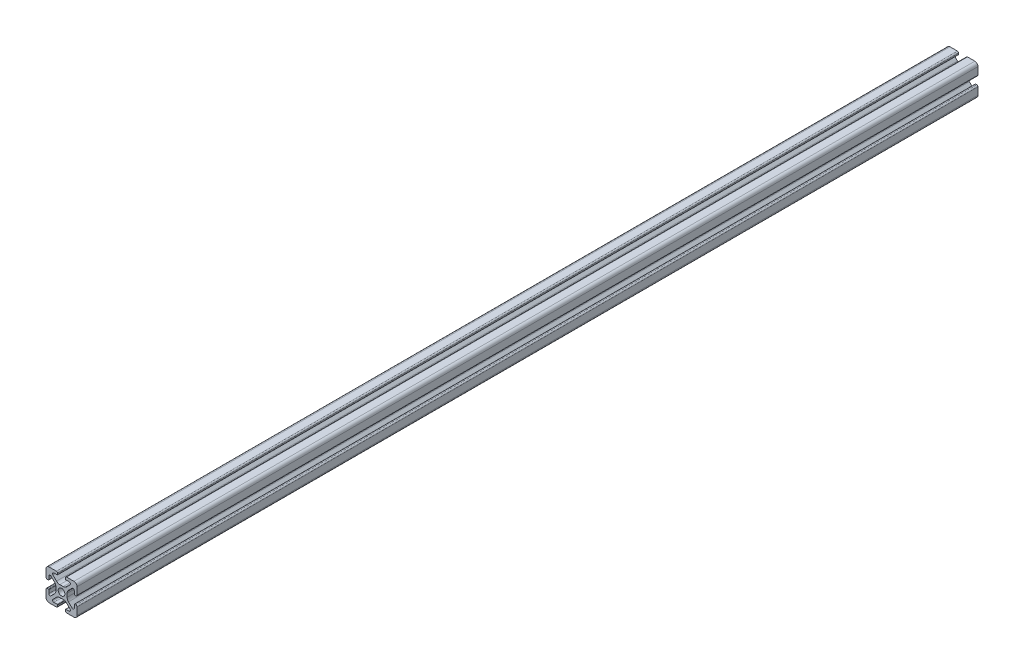
SolidWorks part; units mm, degrees
ref_plane "Front Plane" through (0, 0, 0) normal (0, 0, 1) x (1, 0, 0)
ref_plane "Top Plane" through (0, 0, 0) normal (0, 1, 0) x (1, 0, 0)
ref_plane "Right Plane" through (0, 0, 0) normal (1, 0, 0) x (0, 0, -1)
sketch "Sketch1" plane through (0, 0, 0) normal (0, 0, 1) x (1, 0, 0)
  line L0 (0, 10) -> (0, -10) construction
  line L1 (10, 0) -> (-10, 0) construction
  line L2 (-2.5, 10) -> (2.5, 10) construction
  line L3 (-5.75, 8.2) -> (5.75, 8.2) construction
  circle A0 centre (0, 0) radius 2.15 construction
  point P4 (0, 0)
  point P8 (0, 0)
  point P10 (0, 3.6)
  point P14 (0, 10)
  point P17 (0, 8.2)
  dimension "Thru Hole" = 4.3
  dimension "Height" = 20
  dimension "T Slot Depth" = 6.4
  dimension "T Slot Top Width" = 5
  dimension "T Slot Max Width" = 11.5
  dimension "Wall" = 1.8
sketch "Sketch2" plane through (0, 0, 0) normal (1, 0, 0) x (0, 0, -1)
  line L0 (152.4, 0) -> (-152.4, 0) construction
  point P4 (0, 0)
  dimension "D1" = 304.8
sketch "Sketch3" plane through (0, 0, 0) normal (0, 0, 1) x (1, 0, 0)
  line L0 (3.2874, 10) -> (8, 10)
  line L1 (10, 8) -> (10, -8) construction
  line L2 (8, -10) -> (-8, -10) construction
  line L3 (-10, 10) -> (10, -10) construction
  line L4 (2.5, 9.2126) -> (2.5, 8.5048)
  line L5 (-5.75, 8.2) -> (5.75, 8.2) construction
  line L6 (2.8048, 8.2) -> (4.9118, 8.2)
  line L7 (5.5045, 6.7691) -> (3.2141, 4.4787)
  line L8 (1.0928, 3.6) -> (-1.0928, 3.6)
  line L9 (0, 10) -> (0, -10) construction
  line L10 (5.75, 8.2) -> (5.75, 0) construction
  line L11 (10, 0) -> (-10, 0) construction
  line L12 (0, 0) -> (0, 10) construction
  line L13 (-2.5, 9.2126) -> (-2.5, 8.5048)
  line L14 (-5.5045, 6.7691) -> (-3.2141, 4.4787)
  line L15 (-2.8048, 8.2) -> (-4.9118, 8.2)
  line L16 (-3.2874, 10) -> (-8, 10)
  line L17 (0, 0) -> (-10, 0) construction
  line L18 (-10, 3.2874) -> (-10, 8)
  line L19 (-8.2, 2.8048) -> (-8.2, 4.9118)
  line L20 (-6.7691, 5.5045) -> (-4.4787, 3.2141)
  line L21 (-9.2126, 2.5) -> (-8.5048, 2.5)
  line L22 (-3.6, -1.0928) -> (-3.6, 1.0928)
  line L23 (-6.7691, -5.5045) -> (-4.4787, -3.2141)
  line L24 (-8.2, -2.8048) -> (-8.2, -4.9118)
  line L25 (-9.2126, -2.5) -> (-8.5048, -2.5)
  line L26 (-10, -3.2874) -> (-10, -8)
  line L27 (9.2126, -2.5) -> (8.5048, -2.5)
  line L28 (8.2, -2.8048) -> (8.2, -4.9118)
  line L29 (6.7691, -5.5045) -> (4.4787, -3.2141)
  line L30 (3.6, -1.0928) -> (3.6, 1.0928)
  line L31 (9.2126, 2.5) -> (8.5048, 2.5)
  line L32 (6.7691, 5.5045) -> (4.4787, 3.2141)
  line L33 (8.2, 2.8048) -> (8.2, 4.9118)
  line L34 (10, 8) -> (10, 3.2874)
  line L35 (10, -3.2874) -> (10, -8)
  line L36 (3.2874, -10) -> (8, -10)
  line L37 (-3.2874, -10) -> (-8, -10)
  line L38 (-6.7691, -5.5045) -> (-4.4787, -3.2141)
  line L39 (-2.8048, -8.2) -> (-4.9118, -8.2)
  line L40 (-5.5045, -6.7691) -> (-3.2141, -4.4787)
  line L41 (-2.5, -9.2126) -> (-2.5, -8.5048)
  line L42 (1.0928, -3.6) -> (-1.0928, -3.6)
  line L43 (5.5045, -6.7691) -> (3.2141, -4.4787)
  line L44 (2.8048, -8.2) -> (4.9118, -8.2)
  line L45 (2.5, -9.2126) -> (2.5, -8.5048)
  arc A0 (4.9118, 8.2) -> (5.5045, 6.7691) centre (4.9118, 7.3618) cw
  arc A1 (3.2141, 4.4787) -> (1.0928, 3.6) centre (1.0928, 6.6) cw
  circle A2 centre (0, 0) radius 2.15 construction
  circle A3 centre (0, 0) radius 2.15
  arc A4 (3.2874, 10) -> (2.5, 9.2126) centre (3.2874, 9.2126) ccw
  arc A5 (2.5, 8.5048) -> (2.8048, 8.2) centre (2.8048, 8.5048) ccw
  arc A6 (-3.2874, 10) -> (-2.5, 9.2126) centre (-3.2874, 9.2126) cw
  arc A7 (-4.9118, 8.2) -> (-5.5045, 6.7691) centre (-4.9118, 7.3618) ccw
  arc A8 (-3.2141, 4.4787) -> (-1.0928, 3.6) centre (-1.0928, 6.6) ccw
  arc A9 (-2.5, 8.5048) -> (-2.8048, 8.2) centre (-2.8048, 8.5048) cw
  arc A10 (-8.5048, 2.5) -> (-8.2, 2.8048) centre (-8.5048, 2.8048) ccw
  arc A11 (-4.4787, 3.2141) -> (-3.6, 1.0928) centre (-6.6, 1.0928) cw
  arc A12 (-8.2, 4.9118) -> (-6.7691, 5.5045) centre (-7.3618, 4.9118) cw
  arc A13 (-10, 3.2874) -> (-9.2126, 2.5) centre (-9.2126, 3.2874) ccw
  arc A14 (-8.5048, -2.5) -> (-8.2, -2.8048) centre (-8.5048, -2.8048) cw
  arc A15 (-10, -3.2874) -> (-9.2126, -2.5) centre (-9.2126, -3.2874) cw
  arc A16 (-4.4787, -3.2141) -> (-3.6, -1.0928) centre (-6.6, -1.0928) ccw
  arc A17 (-8.2, -4.9118) -> (-6.7691, -5.5045) centre (-7.3618, -4.9118) ccw
  arc A26 (-8, -10) -> (-10, -8) centre (-8, -8) cw
  arc A27 (-8, 10) -> (-10, 8) centre (-8, 8) ccw
  arc A28 (8, 10) -> (10, 8) centre (8, 8) cw
  arc A29 (10, -8) -> (8, -10) centre (8, -8) cw
  arc A30 (8.2, -4.9118) -> (6.7691, -5.5045) centre (7.3618, -4.9118) cw
  arc A31 (4.4787, -3.2141) -> (3.6, -1.0928) centre (6.6, -1.0928) cw
  arc A32 (10, -3.2874) -> (9.2126, -2.5) centre (9.2126, -3.2874) ccw
  arc A33 (8.5048, -2.5) -> (8.2, -2.8048) centre (8.5048, -2.8048) ccw
  arc A34 (10, 3.2874) -> (9.2126, 2.5) centre (9.2126, 3.2874) cw
  arc A35 (8.2, 4.9118) -> (6.7691, 5.5045) centre (7.3618, 4.9118) ccw
  arc A36 (4.4787, 3.2141) -> (3.6, 1.0928) centre (6.6, 1.0928) ccw
  arc A37 (8.5048, 2.5) -> (8.2, 2.8048) centre (8.5048, 2.8048) cw
  arc A38 (-2.5, -8.5048) -> (-2.8048, -8.2) centre (-2.8048, -8.5048) ccw
  arc A39 (-3.2141, -4.4787) -> (-1.0928, -3.6) centre (-1.0928, -6.6) cw
  arc A40 (-4.9118, -8.2) -> (-5.5045, -6.7691) centre (-4.9118, -7.3618) cw
  arc A41 (-3.2874, -10) -> (-2.5, -9.2126) centre (-3.2874, -9.2126) ccw
  arc A42 (2.5, -8.5048) -> (2.8048, -8.2) centre (2.8048, -8.5048) cw
  arc A43 (3.2874, -10) -> (2.5, -9.2126) centre (3.2874, -9.2126) cw
  arc A44 (3.2141, -4.4787) -> (1.0928, -3.6) centre (1.0928, -6.6) ccw
  arc A45 (4.9118, -8.2) -> (5.5045, -6.7691) centre (4.9118, -7.3618) ccw
  point P36 (2.5, 10)
  point P39 (2.5, 8.2)
  point P49 (0, 3.6)
  point P77 (-3.6, 0)
  point P78 (-8.2, -2.5)
  point P79 (-10, -2.5)
  point P104 (-10, -10)
  point P110 (10, 10)
  point P114 (10, -2.5)
  point P115 (8.2, -2.5)
  point P116 (3.6, 0)
  point P141 (0, -3.6)
  dimension "D1" = 3
  dimension "D2" = 0.8382
  dimension "D4" = 0.7874
  dimension "D5" = 0.3048
  dimension "D6" = 2
  dimension "D3" = 45
extrude "Boss-Extrude1" add sketch "Sketch3" along normal blind 580 contours A45 L44 A42 L45 A43 L36 A29 L35 A32 L27 A33 L28 A30 L29 A31 L30 A36 L32 A35 L33 A37 L31 A34 L34 A28 L0 A4 L4 A5 L6 A0 L7 A1 L8 A8 L14 A7 L15 A9 L13 A6 L16 A27 L18 A13 L21 A10 L19 A12 L20 A11
